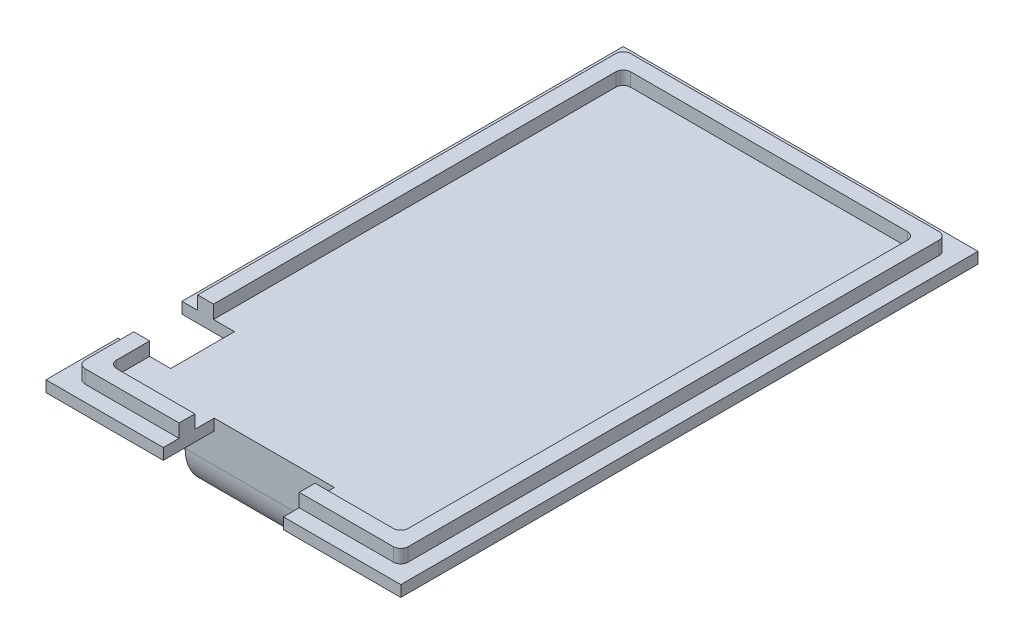
SolidWorks part; units mm, degrees
ref_plane "Front Plane" through (0, 0, 0) normal (0, 0, 1) x (1, 0, 0)
ref_plane "Top Plane" through (0, 0, 0) normal (0, 1, 0) x (1, 0, 0)
ref_plane "Right Plane" through (0, 0, 0) normal (1, 0, 0) x (0, 0, -1)
sketch "PCB Dimensions" plane through (0, 0, 0) normal (0, 1, 0) x (1, 0, 0)
  line L0 (0, 0) -> (-3.5355, 3.5355)
  line L1 (0, 0) -> (40.6457, 0)
  line L2 (0, 0) -> (0, -70.5657)
  line L3 (0, -70.5657) -> (40.6457, -70.5657)
  line L4 (40.6457, 0) -> (40.6457, -70.5657)
  line L5 (40.6457, -70.5657) -> (44.1812, -74.1012)
  line L6 (40.6457, 0) -> (44.1812, 3.5355)
  line L11 (0, -70.5657) -> (-3.5355, -74.1012)
  line L12 (44.1812, -74.1012) -> (-3.5355, -74.1012)
  line L13 (44.1812, -74.1012) -> (44.1812, 3.5355)
  line L14 (44.1812, 3.5355) -> (-3.5355, 3.5355)
  line L15 (-3.5355, -74.1012) -> (-3.5355, 3.5355)
extrude "Boss-Extrude3" add sketch "PCB Dimensions" along normal blind 1.5 contours L14 L15 L12 L13
sketch "Sketch5" plane through (0, 1.5, 0) normal (0, 1, 0) x (1, 0, 0)
  line L11 (-1.4142, 1.4142) -> (42.0599, 1.4142)
  line L12 (-1.4142, 1.4142) -> (-1.4142, -71.9799)
  line L13 (-1.4142, -71.9799) -> (42.0599, -71.9799)
  line L14 (42.0599, 1.4142) -> (42.0599, -71.9799)
  line L17 (0.7071, -0.7071) -> (39.9386, -0.7071)
  line L18 (0.7071, -0.7071) -> (0.7071, -69.8586)
  line L19 (0.7071, -69.8586) -> (39.9386, -69.8586)
  line L20 (39.9386, -0.7071) -> (39.9386, -69.8586)
extrude "Boss-Extrude4" add sketch "Sketch5" along normal blind 1.8 contours L13 L14 L11 L12 | L18 L19 L20 L17
fillet "Fillet1" radius 1 8 edges at (0.7071, 2.4, 69.8586) (-1.4142, 2.4, 71.9799) (39.9386, 2.4, 69.8586) (42.0599, 2.4, 71.9799) (0.7071, 2.4, 0.7071) (39.9386, 2.4, 0.7071) (42.0599, 2.4, -1.4142) (-1.4142, 2.4, -1.4142)
sketch "Sketch6" plane through (0, 0, 0) normal (0, -1, 0) x (1, 0, 0)
  line L0 (8.3228, 67.2497) -> (32.3228, 67.2497)
  line L1 (8.3228, 67.2497) -> (8.3228, 3.2497)
  line L2 (8.3228, 3.2497) -> (32.3228, 3.2497)
  line L3 (32.3228, 67.2497) -> (32.3228, 3.2497)
  line L4 (20.3228, 74.1012) -> (20.3228, -3.5355)
  line L5 (44.1812, 74.1012) -> (-3.5355, 74.1012) construction
  line L6 (44.1812, -3.5355) -> (-3.5355, -3.5355) construction
  line L7 (-3.5355, 35.2828) -> (44.1812, 35.2828)
  line L8 (-3.5355, 74.1012) -> (-3.5355, -3.5355) construction
  line L9 (44.1812, 74.1012) -> (44.1812, -3.5355) construction
extrude "Boss-Extrude5" add sketch "Sketch6" along normal blind 10 contours L1 L7 L4 L0 | L4 L7 L3 L0 | L7 L1 L2 L4 | L7 L4 L2 L3
sketch "Sketch7" plane through (32.3228, 0, 0) normal (1, 0, 0) x (0, 0, -1)
  line L0 (-59.2497, 0) -> (-11.2497, 0)
  line L1 (-59.2497, 0) -> (-59.2497, -6)
  line L2 (-59.2497, -6) -> (-11.2497, -6)
  line L3 (-11.2497, 0) -> (-11.2497, -6)
extrude "Cut-Extrude1" cut sketch "Sketch7" against normal blind 24
fillet "Fillet2" radius 6 2 edges at (20.3228, -10, 3.2497) (20.3228, -10, 67.2497)
fillet "Fillet3" radius 1 2 edges at (20.3228, -6, 11.2497) (20.3228, -6, 59.2497)
scale "Scale1" bodies to scale 112 scale about centroid uniform scaling yes scale factor 0.99
sketch "Sketch8" plane through (0, -0.0322, 0) normal (0, -1, 0) x (1, 0, 0)
  line L1 (43.9426, 73.7128) -> (-3.297, 73.7128) construction
  line L2 (20.3228, 73.7128) -> (12.3228, 73.7128)
  line L3 (20.3228, 73.7128) -> (28.3228, 73.7128)
  line L4 (28.3228, 73.7128) -> (28.3228, 66.9299)
  line L5 (8.4428, 66.9299) -> (32.2028, 66.9299) construction
  line L6 (12.3228, 73.7128) -> (12.3228, 66.9299)
  line L7 (12.3228, 66.9299) -> (28.3228, 66.9299)
extrude "Cut-Extrude2" cut sketch "Sketch8" against normal blind 10
sketch "Sketch9" plane through (0, -0.0322, 0) normal (0, -1, 0) x (1, 0, 0)
  line L1 (-3.297, 55.6128) -> (3.703, 55.6128)
  line L2 (-3.297, 64.1128) -> (-3.297, 55.6128)
  line L3 (-3.297, 64.1128) -> (3.703, 64.1128)
  line L4 (3.703, 64.1128) -> (3.703, 55.6128)
extrude "Cut-Extrude3" cut sketch "Sketch9" against normal blind 10
